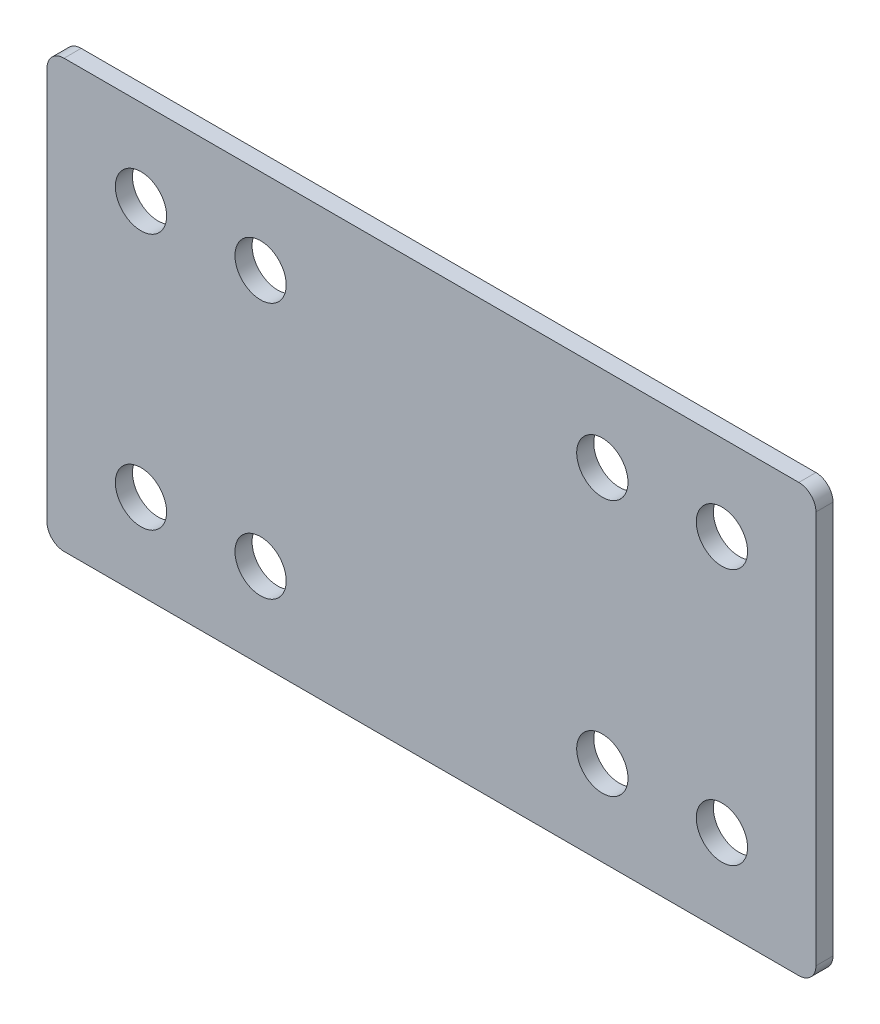
SolidWorks part; units mm, degrees
material "1060 Alloy"
ref_plane "Front Plane" through (0, 0, 0) normal (0, 0, 1) x (1, 0, 0)
ref_plane "Top Plane" through (0, 0, 0) normal (0, 1, 0) x (1, 0, 0)
ref_plane "Right Plane" through (0, 0, 0) normal (1, 0, 0) x (0, 0, -1)
sketch "Sketch1" plane through (0, 0, 0) normal (0, 0, 1) x (1, 0, 0)
  line L1 (-22.5, -12.5) -> (22.5, -12.5)
  line L2 (-22.5, -12.5) -> (-22.5, 12.5)
  line L3 (-22.5, 12.5) -> (22.5, 12.5)
  line L4 (22.5, -12.5) -> (22.5, 12.5)
  line L5 (-22.5, -12.5) -> (22.5, 12.5) construction
  line L6 (-22.5, 12.5) -> (22.5, -12.5) construction
  point P0 (0, 0)
  dimension "D1" = 45
  dimension "D2" = 25
extrude "Boss-Extrude1" add sketch "Sketch1" along normal blind 1
sketch "Sketch2" plane through (0, 0, 1) normal (0, 0, 1) x (1, 0, 0)
  line L0 (0, 0) -> (-10, 0)
  line L1 (0, 0) -> (10, 0)
  line L2 (0, 7.5) -> (10, 7.5)
  line L3 (0, 7.5) -> (-10, 7.5)
  line L4 (0, -7.5) -> (10, -7.5)
  line L5 (0, -7.5) -> (-10, -7.5)
  line L6 (-10, 7.5) -> (-17, 7.5)
  line L7 (10, 7.5) -> (17, 7.5)
  line L8 (-10, -7.5) -> (-17, -7.5)
  line L9 (10, -7.5) -> (17, -7.5)
  circle A0 centre (-10, 7.5) radius 1.5
  circle A1 centre (10, 7.5) radius 1.5
  circle A2 centre (10, -7.5) radius 1.5
  circle A3 centre (-10, -7.5) radius 1.5
  circle A4 centre (-17, 7.5) radius 1.5
  circle A5 centre (-17, -7.5) radius 1.5
  circle A6 centre (17, 7.5) radius 1.5
  circle A7 centre (17, -7.5) radius 1.5
  dimension "D5" = 3
  dimension "D6" = 3
  dimension "D7" = 3
  dimension "D8" = 3
  dimension "D13" = 3
  dimension "D14" = 3
  dimension "D15" = 3
  dimension "D16" = 3
  dimension "D1" = 10
  dimension "D2" = 10
  dimension "D9" = 7
  dimension "D10" = 7
  dimension "D3" = 7.5
  dimension "D4" = 7.5
  dimension "D11" = 15
  dimension "D12" = 15
extrude "Cut-Extrude1" cut sketch "Sketch2" against normal through all
fillet "Fillet1" radius 1 4 edges at (-22.5, -12.5, 0.5) (-22.5, 12.5, 0.5) (22.5, -12.5, 0.5) (22.5, 12.5, 0.5)
